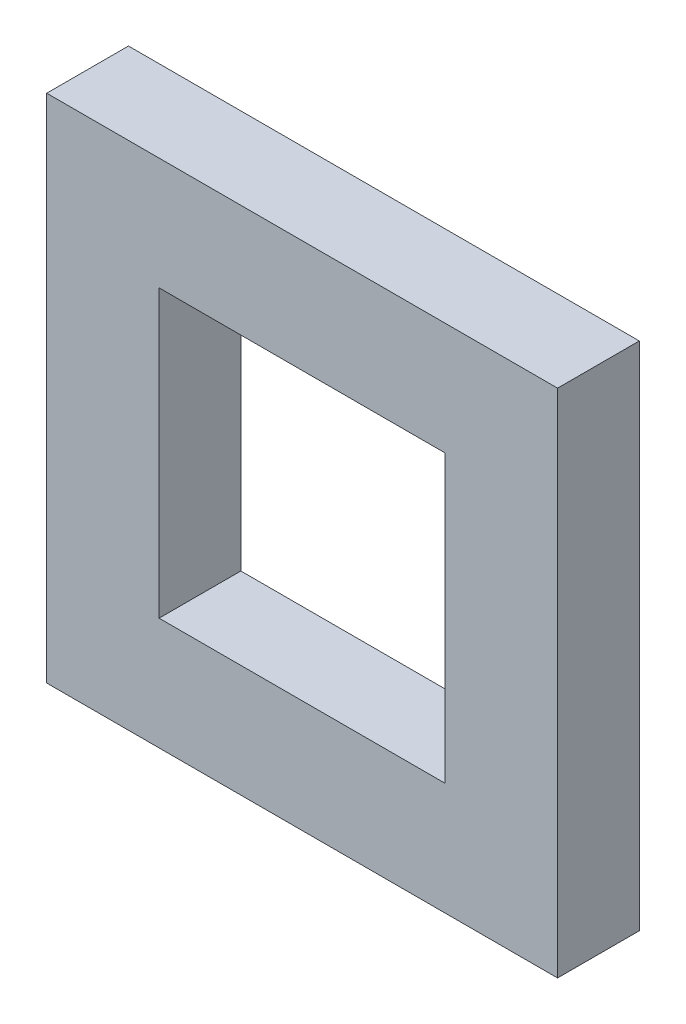
SolidWorks part; units mm, degrees
ref_plane "Front Plane" through (0, 0, 0) normal (0, 0, 1) x (1, 0, 0)
ref_plane "Top Plane" through (0, 0, 0) normal (0, 1, 0) x (1, 0, 0)
ref_plane "Right Plane" through (0, 0, 0) normal (1, 0, 0) x (0, 0, -1)
sketch "Sketch1" plane through (0, 0, 0) normal (0, 0, 1) x (1, 0, 0)
  line L1 (317.5, -317.5) -> (-317.5, -317.5)
  line L2 (317.5, -317.5) -> (317.5, 317.5)
  line L3 (317.5, 317.5) -> (-317.5, 317.5)
  line L4 (-317.5, -317.5) -> (-317.5, 317.5)
  line L5 (317.5, -317.5) -> (-317.5, 317.5) construction
  line L6 (317.5, 317.5) -> (-317.5, -317.5) construction
  point P0 (0, 0)
  dimension "D1" = 635
extrude "Boss-Extrude1" add sketch "Sketch1" along normal blind 101.6 contours L4 L3 L2 L1
sketch "Sketch2" plane through (0, 0, 101.6) normal (0, 0, 1) x (1, 0, 0)
  line L1 (177.8, -177.8) -> (-177.8, -177.8)
  line L2 (177.8, -177.8) -> (177.8, 177.8)
  line L3 (177.8, 177.8) -> (-177.8, 177.8)
  line L4 (-177.8, -177.8) -> (-177.8, 177.8)
  line L5 (177.8, -177.8) -> (-177.8, 177.8) construction
  line L6 (177.8, 177.8) -> (-177.8, -177.8) construction
  point P0 (0, 0)
  dimension "D1" = 355.6
extrude "Cut-Extrude1" cut sketch "Sketch2" against normal blind 101.6
